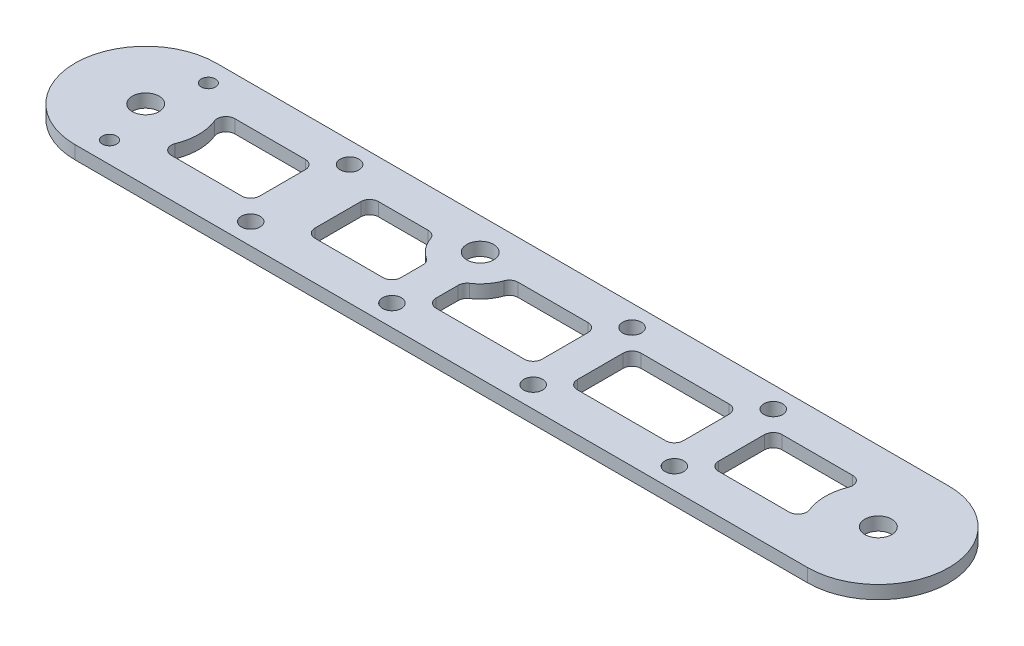
SolidWorks part; units mm, degrees
ref_plane "Front Plane" through (0, 0, 0) normal (0, 0, 1) x (1, 0, 0)
ref_plane "Top Plane" through (0, 0, 0) normal (0, 1, 0) x (1, 0, 0)
ref_plane "Right Plane" through (0, 0, 0) normal (1, 0, 0) x (0, 0, -1)
ref_plane "Plane1" through (0, 4.7625, 0) normal (0, 1, 0) x (1, 0, 0)
sketch "Sketch1" plane through (0, 4.7625, 0) normal (0, 1, 0) x (1, 0, 0)
  line L0 (263.525, 25.4) -> (0, 25.4)
  line L1 (0, -25.4) -> (263.525, -25.4)
  line L2 (166.6875, 11.43) -> (198.4375, 11.43)
  line L3 (201.6125, 8.255) -> (201.6125, -8.255)
  line L4 (198.4375, -11.43) -> (166.6875, -11.43)
  line L5 (163.5125, -8.255) -> (163.5125, 8.255)
  line L6 (122.527, 11.43) -> (147.6375, 11.43)
  line L7 (150.8125, 8.255) -> (150.8125, -8.255)
  line L8 (147.6375, -11.43) -> (115.8875, -11.43)
  line L9 (112.7125, -8.255) -> (112.7125, -0.2857)
  line L10 (72.3066, 11.43) -> (90.198, 11.43)
  line L11 (100.0125, -0.2857) -> (100.0125, -8.255)
  line L12 (96.8375, -11.43) -> (72.3066, -11.43)
  line L13 (69.1316, -8.255) -> (69.1316, 8.255)
  line L14 (20.6351, 11.43) -> (46.0375, 11.43)
  line L15 (49.2125, 8.255) -> (49.2125, -8.255)
  line L16 (46.0375, -11.43) -> (20.6351, -11.43)
  line L17 (242.8899, -11.43) -> (217.4875, -11.43)
  line L18 (214.3125, -8.255) -> (214.3125, 8.255)
  line L19 (217.4875, 11.43) -> (242.8899, 11.43)
  circle A0 centre (0, 0) radius 4.826
  arc A1 (263.525, -25.4) -> (263.525, 25.4) centre (263.525, 0) ccw
  arc A2 (0, 25.4) -> (0, -25.4) centre (0, 0) ccw
  circle A3 centre (263.525, 0) radius 4.826
  circle A4 centre (55.5625, -17.78) radius 3.3782
  circle A5 centre (4.7625, -17.78) radius 2.5527
  circle A6 centre (207.9625, 17.78) radius 3.3782
  circle A7 centre (106.3625, -17.78) radius 3.3782
  circle A8 centre (157.1625, -17.78) radius 3.3782
  circle A9 centre (207.9625, -17.78) radius 3.3782
  circle A10 centre (157.1625, 17.78) radius 3.3782
  circle A11 centre (4.7625, 17.78) radius 2.5527
  circle A12 centre (55.5625, 17.78) radius 3.3782
  circle A13 centre (106.3625, 13.97) radius 4.826
  arc A14 (163.5125, 8.255) -> (166.6875, 11.43) centre (166.6875, 8.255) cw
  arc A15 (198.4375, 11.43) -> (201.6125, 8.255) centre (198.4375, 8.255) cw
  arc A16 (201.6125, -8.255) -> (198.4375, -11.43) centre (198.4375, -8.255) cw
  arc A17 (166.6875, -11.43) -> (163.5125, -8.255) centre (166.6875, -8.255) cw
  arc A18 (119.5335, 9.3133) -> (122.527, 11.43) centre (122.527, 8.255) cw
  arc A19 (147.6375, 11.43) -> (150.8125, 8.255) centre (147.6375, 8.255) cw
  arc A20 (150.8125, -8.255) -> (147.6375, -11.43) centre (147.6375, -8.255) cw
  arc A21 (115.8875, -11.43) -> (112.7125, -8.255) centre (115.8875, -8.255) cw
  arc A22 (112.7125, -0.2857) -> (114.1236, 2.3542) centre (115.8875, -0.2857) cw
  arc A23 (114.1236, 2.3542) -> (119.5335, 9.3133) centre (106.3625, 13.97) ccw
  arc A24 (90.198, 11.43) -> (93.1915, 9.3133) centre (90.198, 8.255) cw
  arc A25 (93.1915, 9.3133) -> (98.6014, 2.3542) centre (106.3625, 13.97) ccw
  arc A26 (98.6014, 2.3542) -> (100.0125, -0.2857) centre (96.8375, -0.2857) cw
  arc A27 (100.0125, -8.255) -> (96.8375, -11.43) centre (96.8375, -8.255) cw
  arc A28 (72.3066, -11.43) -> (69.1316, -8.255) centre (72.3066, -8.255) cw
  arc A29 (69.1316, 8.255) -> (72.3066, 11.43) centre (72.3066, 8.255) cw
  arc A30 (17.6872, 7.0757) -> (20.6351, 11.43) centre (20.6351, 8.255) cw
  arc A31 (46.0375, 11.43) -> (49.2125, 8.255) centre (46.0375, 8.255) cw
  arc A32 (49.2125, -8.255) -> (46.0375, -11.43) centre (46.0375, -8.255) cw
  arc A33 (20.6351, -11.43) -> (17.6872, -7.0757) centre (20.6351, -8.255) cw
  arc A34 (17.6872, -7.0757) -> (17.6872, 7.0757) centre (0, 0) ccw
  arc A35 (245.8378, -7.0757) -> (242.8899, -11.43) centre (242.8899, -8.255) cw
  arc A36 (217.4875, -11.43) -> (214.3125, -8.255) centre (217.4875, -8.255) cw
  arc A37 (214.3125, 8.255) -> (217.4875, 11.43) centre (217.4875, 8.255) cw
  arc A38 (242.8899, 11.43) -> (245.8378, 7.0757) centre (242.8899, 8.255) cw
  arc A39 (245.8378, 7.0757) -> (245.8378, -7.0757) centre (263.525, 0) ccw
extrude "Boss-Extrude1" add sketch "Sketch1" against normal blind 4.7625
